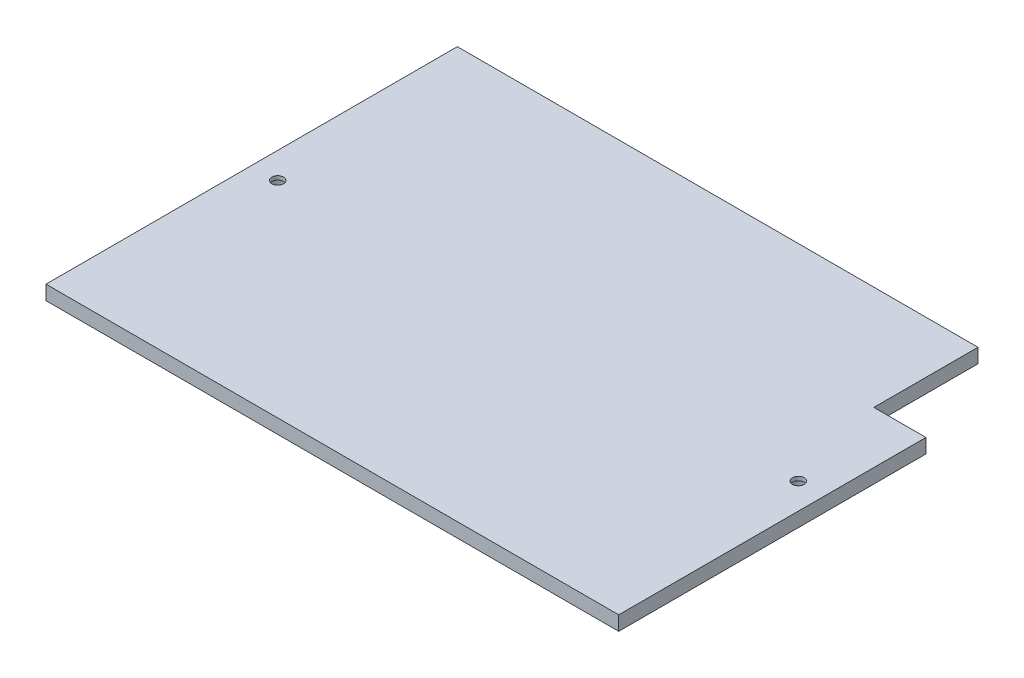
SolidWorks part; units mm, degrees
ref_plane "Front Plane" through (0, 0, 0) normal (0, 0, 1) x (1, 0, 0)
ref_plane "Top Plane" through (0, 0, 0) normal (0, 1, 0) x (1, 0, 0)
ref_plane "Right Plane" through (0, 0, 0) normal (1, 0, 0) x (0, 0, -1)
sketch "Sketch1" plane through (0, 0, 0) normal (0, 1, 0) x (1, 0, 0)
  line L1 (-110, 79) -> (110, 79)
  line L2 (-110, 79) -> (-110, -79)
  line L3 (-110, -79) -> (110, -79)
  line L4 (110, 79) -> (110, -79)
  line L5 (-110, 79) -> (110, -79) construction
  line L6 (-110, -79) -> (110, 79) construction
  point P0 (0, 0)
  dimension "D1" = 220
  dimension "D2" = 158
extrude "Boss-Extrude1" add sketch "Sketch1" along normal blind 5.5
sketch "Sketch2" plane through (0, 0, 0) normal (0, 1, 0) x (1, 0, 0)
  point P0 (100, 0)
  dimension "D1" = 100
sketch "Sketch4" [suppressed] plane through (0, 4, 0) normal (0, 1, 0) x (1, 0, 0)
  line L0 (115, -79) -> (115, -59)
  line L1 (115, -79) -> (115, 79) construction
  line L2 (115, -79) -> (95, -79)
  line L3 (-115, -79) -> (115, -79) construction
  line L4 (115, -59) -> (85.4514, -59) construction
  arc A0 (95, -79) -> (115, -59) centre (115, -79) cw
  dimension "D1" = 20
hole_wizard "CBORE for M4 SHCS1" positions "Sketch2" profile "Sketch5" counterbore size "M4" standard "ANSI Metric" end condition through all
sketch "Sketch5" plane through (100, 0, 0) normal (1, 0, 0) x (0, 0, -1)
  line L0 (0, 0) -> (0, 5.5)
  line L1 (0, 5.5) -> (2.25, 5.5)
  line L3 (2.25, 5.5) -> (2.25, 4)
  line L4 (2.25, 4) -> (4, 4)
  line L5 (4, 4) -> (4, 0)
  line L7 (4, 0) -> (0, 0)
  line L11 (0, -6.35) -> (0, 107.95) construction
  dimension "Thru Hole Dia." = 4.5
  dimension "Thru Hole Depth" = 5.5
  dimension "C'Bore Dia." = 8
  dimension "C'Bore Depth" = 4
mirror "Mirror2" about plane through (0, 0, 0) normal (1, 0, 0) of "CBORE for M4 SHCS1"
sketch "Sketch6" plane through (0, 5.5, 0) normal (0, 1, 0) x (1, 0, 0)
  line L1 (110, 79) -> (90, 79)
  line L2 (110, 79) -> (110, 39)
  line L3 (110, 39) -> (90, 39)
  line L4 (90, 79) -> (90, 39)
  dimension "D1" = 20
  dimension "D2" = 40
extrude "Cut-Extrude2" cut sketch "Sketch6" against normal through all
